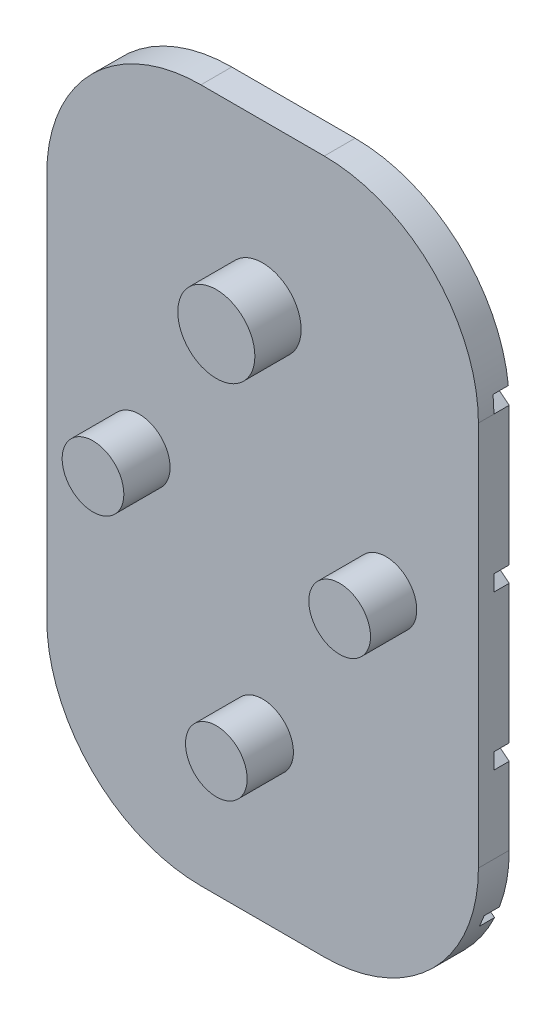
SolidWorks part; units mm, degrees
ref_plane "Alzado" through (0, 0, 0) normal (0, 0, 1) x (1, 0, 0)
ref_plane "Planta" through (0, 0, 0) normal (0, 1, 0) x (1, 0, 0)
ref_plane "Vista lateral" through (0, 0, 0) normal (1, 0, 0) x (0, 0, -1)
sketch "Croquis1" plane through (0, 0, 0) normal (0, 0, 1) x (1, 0, 0)
  line L0 (14, 0) -> (-14, 0) construction
  line L1 (-4, -22.5) -> (4, -22.5)
  line L2 (-14, -12.5) -> (-14, 12.5)
  line L3 (-4, 22.5) -> (4, 22.5)
  line L4 (14, -12.5) -> (14, 12.5)
  line L7 (0, 22.5) -> (0, -22.5) construction
  circle A0 centre (0, 12) radius 2.5
  circle A1 centre (0, -12) radius 2
  circle A2 centre (-8, 0) radius 2
  circle A3 centre (8, 0) radius 2
  arc A4 (4, 22.5) -> (14, 12.5) centre (4, 12.5) cw
  arc A5 (4, -22.5) -> (14, -12.5) centre (4, -12.5) ccw
  arc A6 (-4, -22.5) -> (-14, -12.5) centre (-4, -12.5) cw
  arc A7 (-14, 12.5) -> (-4, 22.5) centre (-4, 12.5) cw
  point P0 (0, 0)
  point P25 (14, 22.5)
  point P28 (14, -22.5)
  point P33 (-14, 22.5)
  dimension "D1" = 5
  dimension "D2" = 4
  dimension "D7" = 10
  dimension "D3" = 12
  dimension "D4" = 8
  dimension "D5" = 45
  dimension "D6" = 28
extrude "Saliente-Extruir1" add sketch "Croquis1" along normal blind 2
sketch "Croquis2" plane through (0, 0, 2) normal (0, 0, 1) x (1, 0, 0)
  line L4 (4, 22.5) -> (-4, 22.5)
  line L5 (-14, 12.5) -> (-14, -12.5)
  line L6 (-4, -22.5) -> (4, -22.5)
  line L7 (14, -12.5) -> (14, 12.5)
  line L8 (4, 22.5) -> (-4, 22.5)
  line L9 (-14, 12.5) -> (-14, -12.5)
  line L10 (-4, -22.5) -> (4, -22.5)
  line L11 (14, -12.5) -> (14, 12.5)
  circle A0 centre (8, 0) radius 2 construction
  circle A1 centre (0, -12) radius 2 construction
  circle A2 centre (-8, 0) radius 2 construction
  circle A3 centre (0, 12) radius 2.5 construction
  arc A4 (14, 12.5) -> (4, 22.5) centre (4, 12.5) ccw
  arc A5 (-4, 22.5) -> (-14, 12.5) centre (-4, 12.5) ccw
  arc A6 (-14, -12.5) -> (-4, -22.5) centre (-4, -12.5) ccw
  arc A7 (4, -22.5) -> (14, -12.5) centre (4, -12.5) ccw
  arc A8 (14, 12.5) -> (4, 22.5) centre (4, 12.5) ccw
  arc A9 (-4, 22.5) -> (-14, 12.5) centre (-4, 12.5) ccw
  arc A10 (-14, -12.5) -> (-4, -22.5) centre (-4, -12.5) ccw
  arc A11 (4, -22.5) -> (14, -12.5) centre (4, -12.5) ccw
  circle A15 centre (8, 0) radius 2
  circle A16 centre (0, -12) radius 2
  circle A17 centre (-8, 0) radius 2
  circle A18 centre (0, 12) radius 2.5
  circle A19 centre (0, 12) radius 1.7
  circle A20 centre (-8, 0) radius 1.2
  circle A21 centre (8, 0) radius 1.2
  circle A22 centre (0, -12) radius 1.2
  circle M20 centre (8, 0) radius 2
  dimension "D1" = 0
  dimension "D2" = 0.8
extrude "Saliente-Extruir2" add sketch "Croquis2" along normal blind 3 separate body contours A21 M20 | A17 | A16 | A18
sketch "Croquis3" plane through (0, 0, 0) normal (0, 0, -1) x (-1, 0, 0)
  line L0 (0, 17.5799) -> (0, -24.2516) construction
  line L1 (-14, -12.5) -> (-14, 12.5) construction
  line L2 (14, 12.5) -> (14, 2.5) construction
  line L6 (-14, 12.5) -> (-14, -12.5)
  line L7 (-4, -22.5) -> (4, -22.5)
  line L8 (14, -12.5) -> (14, 12.5)
  line L9 (4, 22.5) -> (-4, 22.5)
  line L10 (-14, 12.5) -> (-14, -12.5)
  line L11 (-4, -22.5) -> (4, -22.5)
  line L12 (14, -12.5) -> (14, 12.5)
  line L13 (4, 22.5) -> (-4, 22.5)
  arc A0 (14.513, 13.1138) -> (-14.513, 13.1138) centre (0, -4.2516) ccw construction
  arc A1 (14, 12.5) -> (-14, 12.5) centre (0, -4.2516) ccw construction
  arc A2 (14, 12.5) -> (-14, 12.5) centre (0, -4.2516) ccw
  arc A3 (-4, 22.5) -> (-14, 12.5) centre (-4, 12.5) ccw construction
  arc A4 (13.942, 13.5756) -> (-13.942, 13.5756) centre (0, -4.2516) ccw
  arc A5 (14, 2.5) -> (-14, 2.5) centre (0, -14.2516) ccw
  arc A6 (14, 3.53) -> (-14, 3.53) centre (0, -14.2516) ccw
  circle A7 centre (0, -12) radius 2 construction
  arc A8 (14, -7.5) -> (-14, -7.5) centre (0, -24.2516) ccw
  arc A9 (-4, 22.5) -> (-14, 12.5) centre (-4, 12.5) ccw
  arc A10 (-14, -12.5) -> (-4, -22.5) centre (-4, -12.5) ccw
  arc A11 (4, -22.5) -> (14, -12.5) centre (4, -12.5) ccw
  arc A12 (14, 12.5) -> (4, 22.5) centre (4, 12.5) ccw
  arc A13 (-4, 22.5) -> (-14, 12.5) centre (-4, 12.5) ccw
  arc A14 (-14, -12.5) -> (-4, -22.5) centre (-4, -12.5) ccw
  arc A15 (4, -22.5) -> (14, -12.5) centre (4, -12.5) ccw
  arc A16 (14, 12.5) -> (4, 22.5) centre (4, 12.5) ccw
  arc A17 (14, -6.47) -> (-14, -6.47) centre (0, -24.2516) ccw
  circle A18 centre (0, -12) radius 2
  arc A19 (13.0515, -16.7509) -> (-13.0515, -16.7509) centre (0, -34.2516) ccw
  arc A20 (13.3705, -15.9919) -> (-13.3705, -15.9919) centre (0, -34.2516) ccw
  arc A22 (14, 2.5) -> (4, 12.5) centre (4, 2.5) ccw [skipped]
  arc A23 (14, -7.5) -> (4, 2.5) centre (4, -7.5) ccw [skipped]
  arc A24 (14, -17.5) -> (4, -7.5) centre (4, -17.5) ccw [skipped]
  arc M11 (-4, 22.5) -> (-14, 12.5) centre (-4, 12.5) ccw
  line M12 (-14, 12.5) -> (-14, -12.5)
  arc M17 (14, 12.5) -> (4, 22.5) centre (4, 12.5) ccw
  dimension "D1" = 21.8315
  dimension "D2" = 0.8
  dimension "D5" = 10
  dimension "D3" = 0
  dimension "D4" = 4
extrude "Cortar-Extruir1" cut sketch "Croquis3" against normal blind 1 contours A15 A20 A18 A19 | A18 A20 A14 A19 | L12 A17 A8 M12 | L12 A6 L10 A5 | A4 A2 M17 M11
